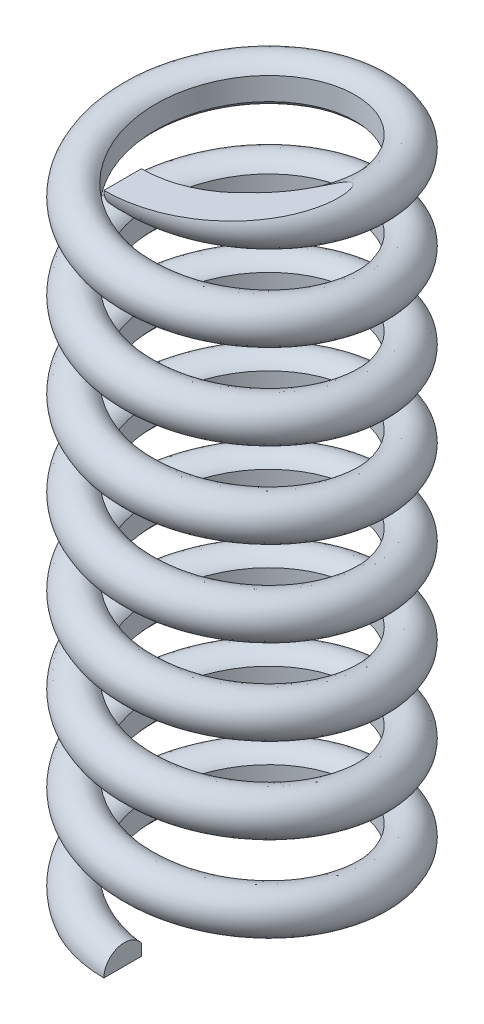
SolidWorks part; units mm, degrees
ref_plane "Front Plane" through (0, 0, 0) normal (0, 0, 1) x (1, 0, 0)
ref_plane "Top Plane" through (0, 0, 0) normal (0, 1, 0) x (1, 0, 0)
ref_plane "Right Plane" through (0, 0, 0) normal (1, 0, 0) x (0, 0, -1)
sketch "Sketch1" plane through (0, 0, 0) normal (0, 1, 0) x (1, 0, 0)
  circle A0 centre (0, 0) radius 3.45
  dimension "D1" = 6.9
curve "Helix/Spiral1" pitch 2.5 height 20 turns 8
sketch "Sketch2" plane through (0, 0, 0) normal (1, 0, 0) x (0, 0, -1)
  circle A0 centre (-3.45, 0) radius 0.6
  spline S0 degree 3 poles (-3.45, 0) (-3.45, 0.0518) (-3.2704, 0.1564) (-2.503, 0.3125) (-1.3546, 0.4688) (0, 0.625) (1.3546, 0.7813) (2.503, 0.9375) (3.2704, 1.0938) (3.5398, 1.25) (3.2704, 1.4063) (2.503, 1.5625) (1.3546, 1.7188) (0, 1.875) (-1.3546, 2.0313) (-2.503, 2.1875) (-3.2704, 2.3438) (-3.5398, 2.5) (-3.2704, 2.6563) (-2.503, 2.8125) (-1.3546, 2.9688) (0, 3.125) (1.3546, 3.2813) (2.503, 3.4375) (3.2704, 3.5938) (3.5398, 3.75) (3.2704, 3.9063) (2.503, 4.0625) (1.3546, 4.2188) (0, 4.375) (-1.3546, 4.5312) (-2.503, 4.6875) (-3.2704, 4.8438) (-3.5398, 5) (-3.2704, 5.1563) (-2.503, 5.3125) (-1.3546, 5.4688) (0, 5.625) (1.3546, 5.7813) (2.503, 5.9375) (3.2704, 6.0938) (3.5398, 6.25) (3.2704, 6.4063) (2.503, 6.5625) (1.3546, 6.7188) (0, 6.875) (-1.3546, 7.0313) (-2.503, 7.1875) (-3.2704, 7.3438) (-3.5398, 7.5) (-3.2704, 7.6563) (-2.503, 7.8125) (-1.3546, 7.9688) (0, 8.125) (1.3546, 8.2813) (2.503, 8.4375) (3.2704, 8.5938) (3.5398, 8.75) (3.2704, 8.9063) (2.503, 9.0625) (1.3546, 9.2188) (0, 9.375) (-1.3546, 9.5313) (-2.503, 9.6875) (-3.2704, 9.8438) (-3.5398, 10) (-3.2704, 10.1563) (-2.503, 10.3125) (-1.3546, 10.4688) (0, 10.625) (1.3546, 10.7813) (2.503, 10.9375) (3.2704, 11.0938) (3.5398, 11.25) (3.2704, 11.4063) (2.503, 11.5625) (1.3546, 11.7188) (0, 11.875) (-1.3546, 12.0313) (-2.503, 12.1875) (-3.2704, 12.3438) (-3.5398, 12.5) (-3.2704, 12.6563) (-2.503, 12.8125) (-1.3546, 12.9688) (0, 13.125) (1.3546, 13.2813) (2.503, 13.4375) (3.2704, 13.5938) (3.5398, 13.75) (3.2704, 13.9063) (2.503, 14.0625) (1.3546, 14.2188) (0, 14.375) (-1.3546, 14.5313) (-2.503, 14.6875) (-3.2704, 14.8438) (-3.5398, 15) (-3.2704, 15.1563) (-2.503, 15.3125) (-1.3546, 15.4688) (0, 15.625) (1.3546, 15.7813) (2.503, 15.9375) (3.2704, 16.0938) (3.5398, 16.25) (3.2704, 16.4063) (2.503, 16.5625) (1.3546, 16.7188) (0, 16.875) (-1.3546, 17.0313) (-2.503, 17.1875) (-3.2704, 17.3437) (-3.5398, 17.5) (-3.2704, 17.6562) (-2.503, 17.8125) (-1.3546, 17.9687) (0, 18.125) (1.3546, 18.2812) (2.503, 18.4375) (3.2704, 18.5937) (3.5398, 18.75) (3.2704, 18.9062) (2.503, 19.0625) (1.3546, 19.2187) (0, 19.375) (-1.3546, 19.5312) (-2.503, 19.6875) (-3.2704, 19.8436) (-3.45, 19.9482) (-3.45, 20) knots 0 0 0 0 0.007813 0.015625 0.023438 0.03125 0.039063 0.046875 0.054688 0.0625 0.070313 0.078125 0.085938 0.09375 0.101563 0.109375 0.117188 0.125 0.132813 0.140625 0.148438 0.15625 0.164063 0.171875 0.179688 0.1875 0.195313 0.203125 0.210938 0.21875 0.226563 0.234375 0.242188 0.25 0.257813 0.265625 0.273438 0.28125 0.289063 0.296875 0.304688 0.3125 0.320313 0.328125 0.335938 0.34375 0.351563 0.359375 0.367188 0.375 0.382813 0.390625 0.398438 0.40625 0.414063 0.421875 0.429688 0.4375 0.445313 0.453125 0.460938 0.46875 0.476563 0.484375 0.492188 0.5 0.507813 0.515625 0.523438 0.53125 0.539063 0.546875 0.554688 0.5625 0.570313 0.578125 0.585938 0.59375 0.601563 0.609375 0.617188 0.625 0.632813 0.640625 0.648438 0.65625 0.664063 0.671875 0.679688 0.6875 0.695313 0.703125 0.710938 0.71875 0.726563 0.734375 0.742188 0.75 0.757813 0.765625 0.773438 0.78125 0.789063 0.796875 0.804688 0.8125 0.820313 0.828125 0.835938 0.84375 0.851563 0.859375 0.867188 0.875 0.882813 0.890625 0.898438 0.90625 0.914063 0.921875 0.929688 0.9375 0.945313 0.953125 0.960938 0.96875 0.976563 0.984375 0.992188 1 1 1 1 construction
  dimension "D1" = 1.2
sweep "Sweep1" add profiles "Sketch2" path "Helix/Spiral1"
sketch "Sketch3" plane through (0, 0, 0) normal (1, 0, 0) x (0, 0, -1)
  line L1 (-5, 0) -> (5, 0)
  line L2 (-5, 0) -> (-5, -1)
  line L3 (-5, -1) -> (5, -1)
  line L4 (5, 0) -> (5, -1)
  circle A1 centre (-3.45, 0) radius 0.6
  circle A2 centre (-3.45, 0) radius 0.6 construction
  dimension "D2" = 10
  dimension "D3" = 5
  dimension "D4" = 1
  dimension "D1" = 0
extrude "Cut-Extrude1" cut sketch "Sketch3" against normal blind 43
sketch "Sketch4" plane through (0, 0, 0) normal (-1, 0, 0) x (0, 0, 1)
  line L1 (-5, 21) -> (5, 21)
  line L2 (-5, 21) -> (-5, 20)
  line L3 (-5, 20) -> (5, 20)
  line L4 (5, 21) -> (5, 20)
  circle A1 centre (3.45, 20) radius 0.6
  circle A2 centre (3.45, 20) radius 0.6 construction
  dimension "D2" = 10
  dimension "D3" = 5
  dimension "D4" = 1
  dimension "D1" = 0
extrude "Cut-Extrude2" cut sketch "Sketch4" against normal blind 43
sketch "Sketch5" plane through (0, 0, 0) normal (0, 1, 0) x (1, 0, 0)
  circle A0 centre (0, 0) radius 2.95
  dimension "D1" = 5.9
extrude "Cut-Extrude4" cut sketch "Sketch5" against normal through all both and the other way through all
